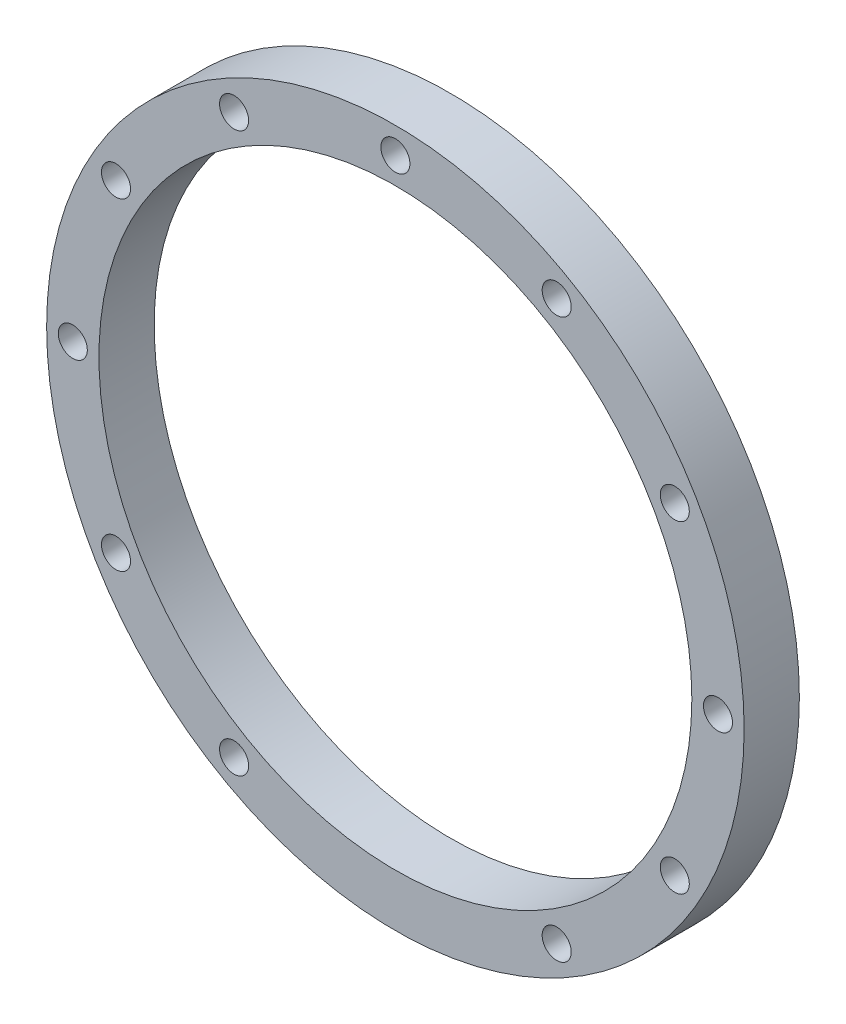
SolidWorks part; units mm, degrees
material "ABS"
ref_plane "Plano frontal" through (0, 0, 0) normal (0, 0, 1) x (1, 0, 0)
ref_plane "Plano superior" through (0, 0, 0) normal (0, 1, 0) x (1, 0, 0)
ref_plane "Plano direito" through (0, 0, 0) normal (1, 0, 0) x (0, 0, -1)
sketch "Esboço1" plane through (0, 0, 0) normal (0, 0, 1) x (1, 0, 0)
  circle A0 centre (0, 0) radius 60
  dimension "D1" = 120
extrude "Ressalto-extrusão1" add sketch "Esboço1" along normal blind 9.5
sketch "Esboço2" plane through (0, 0, 9.5) normal (0, 0, 1) x (1, 0, 0)
  line L0 (0, -70.9271) -> (0, 67.1998) construction
  line L1 (-65.7747, 0) -> (67.748, 0) construction
  circle A0 centre (0, 0) radius 51
  circle A1 centre (0, 55.5) radius 2.5
  circle A2 centre (27.75, 48.0644) radius 2.5
  circle A3 centre (48.0644, 27.75) radius 2.5
  circle A4 centre (55.5, 0) radius 2.5
  circle A5 centre (48.0644, -27.75) radius 2.5
  circle A6 centre (27.75, -48.0644) radius 2.5
  circle A8 centre (-27.75, -48.0644) radius 2.5
  circle A9 centre (-48.0644, -27.75) radius 2.5
  circle A10 centre (-55.5, 0) radius 2.5
  circle A11 centre (-48.0644, 27.75) radius 2.5
  circle A12 centre (-27.75, 48.0644) radius 2.5
  circle A13 centre (0, -55.5) radius 2.5 [skipped]
  dimension "D1" = 102
  dimension "D3" = 5
  dimension "D2" = 55.5
  dimension "D4" = 12
extrude "Corte-extrusão1" cut sketch "Esboço2" against normal through all
